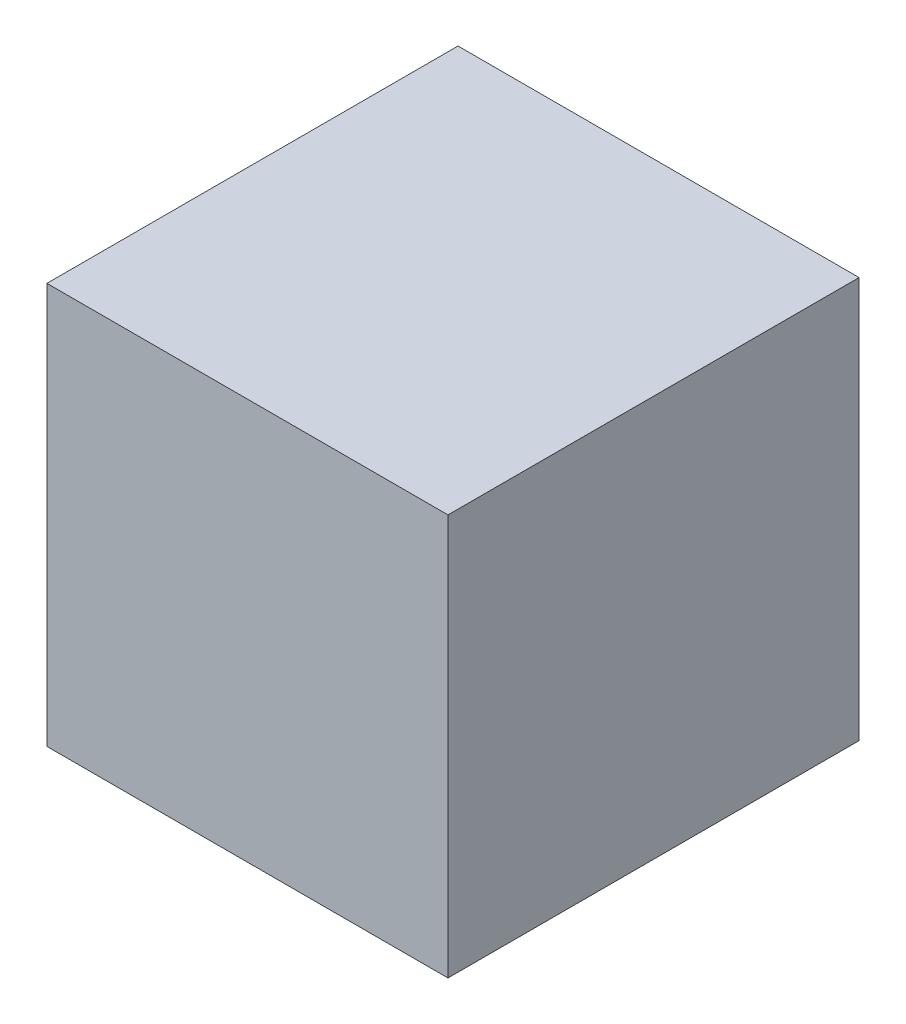
SolidWorks part; units mm, degrees
material "ABS"
ref_plane "Front Plane" through (0, 0, 0) normal (0, 0, 1) x (1, 0, 0)
ref_plane "Top Plane" through (0, 0, 0) normal (0, 1, 0) x (1, 0, 0)
ref_plane "Right Plane" through (0, 0, 0) normal (1, 0, 0) x (0, 0, -1)
sketch "Sketch1" plane through (0, 0, 0) normal (0, 0, 1) x (1, 0, 0)
  line L1 (-100, 100) -> (100, 100)
  line L2 (-100, 100) -> (-100, -100)
  line L3 (-100, -100) -> (100, -100)
  line L4 (100, 100) -> (100, -100)
  line L5 (-100, 100) -> (100, -100) construction
  line L6 (-100, -100) -> (100, 100) construction
  line L7 (95, 95) -> (-95, 95)
  line L8 (95, 95) -> (95, -95)
  line L9 (95, -95) -> (-95, -95)
  line L10 (-95, 95) -> (-95, -95)
  line L11 (95, 95) -> (-95, -95) construction
  line L12 (95, -95) -> (-95, 95) construction
  point P0 (0, 0)
  point P6 (0, 0)
  dimension "D1" = 200
  dimension "D2" = 5
extrude "Boss-Extrude1" add sketch "Sketch1" along normal blind 200
sketch "Sketch2" plane through (0, 0, 200) normal (0, 0, 1) x (1, 0, 0)
  line L1 (-100, -100) -> (100, -100)
  line L2 (-100, -100) -> (-100, 100)
  line L3 (-100, 100) -> (100, 100)
  line L4 (100, -100) -> (100, 100)
  line L5 (-100, -100) -> (100, 100) construction
  line L6 (-100, 100) -> (100, -100) construction
  point P0 (0, 0)
extrude "Boss-Extrude2" add sketch "Sketch2" along normal blind 5
sketch "Sketch3" plane through (0, -100, 0) normal (0, -1, 0) x (1, 0, 0)
  line L0 (13, 5) -> (-13, 5) construction
  line L3 (-100, 0) -> (100, 0) construction
  circle A0 centre (13, 5) radius 2.5
  circle A1 centre (-13, 5) radius 2.5
  point P2 (0, 0)
  point P3 (0, 5)
  dimension "D1" = 5
  dimension "D2" = 26
  dimension "D3" = 5
extrude "Cut-Extrude1" cut sketch "Sketch3" against normal blind 6
